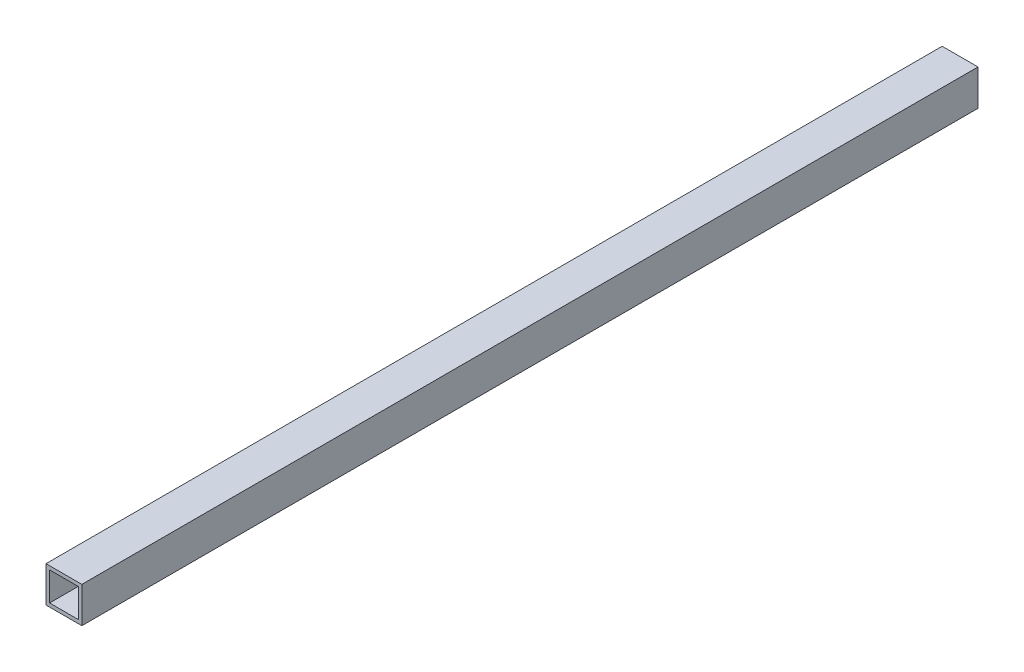
SolidWorks part; units mm, degrees
material "1.0037 (S235JR)"
ref_plane "Front Plane" through (0, 0, 0) normal (0, 0, 1) x (1, 0, 0)
ref_plane "Top Plane" through (0, 0, 0) normal (0, 1, 0) x (1, 0, 0)
ref_plane "Right Plane" through (0, 0, 0) normal (1, 0, 0) x (0, 0, -1)
curve "Curve1"
  spline degree 1 poles (0, 0, -500) (0, 0, 500) knots 0 0 1 1
sketch "Sketch1" plane through (0, 0, 0) normal (0, 0, 1) x (1, 0, 0)
  line L0 (0, 35.3535) -> (0, -33.8384) construction
  line L1 (-20, 20) -> (20, 20)
  line L2 (-20, 20) -> (-20, -20)
  line L3 (-20, -20) -> (20, -20)
  line L4 (20, 20) -> (20, -20)
  line L5 (-16, 16) -> (16, 16)
  line L6 (-16, 16) -> (-16, -16)
  line L7 (-16, -16) -> (16, -16)
  line L8 (16, 16) -> (16, -16)
  line L9 (-39.3939, 0) -> (41.5152, 0) construction
  dimension "D1" = 40
  dimension "D2" = 32
sweep "Sweep1" add profiles "Sketch1" path "Curve1"
